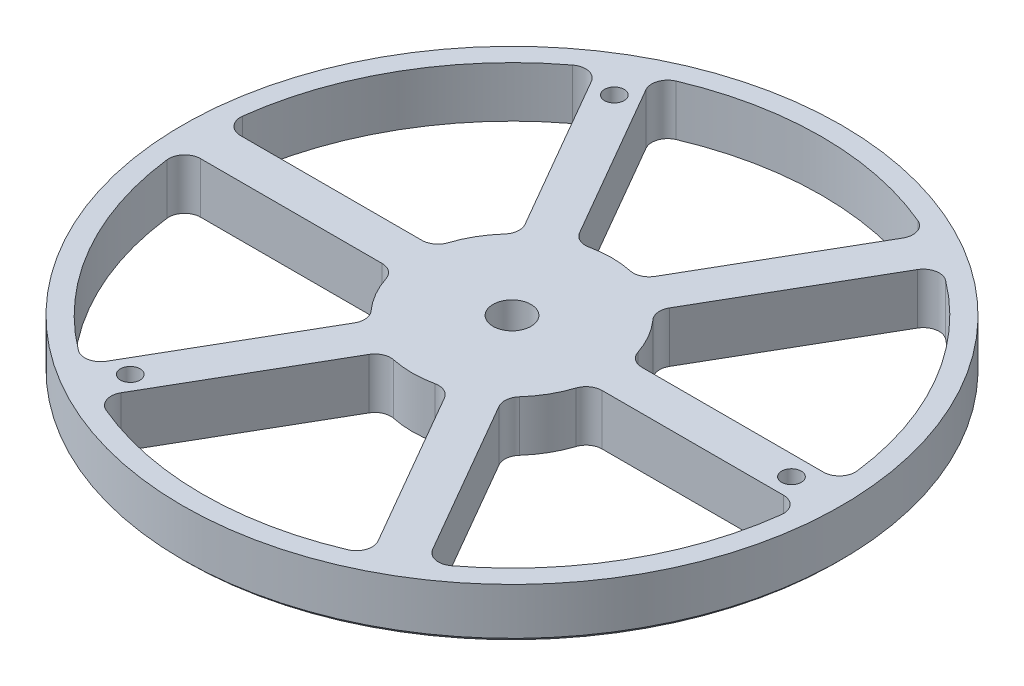
SolidWorks part; units mm, degrees
material "6061-T6 (SS)"
ref_plane "Front Plane" through (0, 0, 0) normal (0, 0, 1) x (1, 0, 0)
ref_plane "Top Plane" through (0, 0, 0) normal (0, 1, 0) x (1, 0, 0)
ref_plane "Right Plane" through (0, 0, 0) normal (1, 0, 0) x (0, 0, -1)
sketch "Sketch2" plane through (0, 0, 0) normal (1, 0, 0) x (0, 0, -1)
  line L0 (0, 0) -> (-82.55, 0)
  line L1 (-82.55, 0) -> (-82.55, 12.7)
  line L2 (-82.55, 12.7) -> (0, 12.7)
  line L5 (0, 12.7) -> (0, 0)
  dimension "D1" = 82.55
  dimension "D2" = 12.7
ref_axis "Axis1" through (0, -0.635, 0) along (0, 1, 0)
revolve "Revolve1" add sketch "Sketch2" angle 360 about axis through (0, -0.635, 0) along (0, 1, 0)
hole_wizard "#10 (0.1935) Diameter Hole1" positions "Sketch6" profile "Sketch7" hole size "#10" standard "ANSI Inch" end condition through all
sketch "Sketch6" plane through (0, 12.7, 0) normal (0, 1, 0) x (1, 0, 0)
  line L0 (0, 0) -> (-69.8201, 120.932) construction
  line L2 (0, 0) -> (0, 109.0908) construction
  point P0 (-35, 60.6218)
  dimension "D1" = 30
  dimension "D2" = 70
sketch "Sketch7" plane through (-35, 12.7, -60.6218) normal (1, 0, 0) x (0, 0, 1)
  line L0 (0, 0) -> (0, 12.7)
  line L1 (0, 12.7) -> (2.4574, 12.7)
  line L2 (2.4574, 12.7) -> (2.4574, 0)
  line L5 (2.4574, 0) -> (0, 0)
  line L11 (0, -6.35) -> (0, 107.95) construction
  dimension "Thru Hole Dia." = 4.9149
  dimension "Thru Hole Depth" = 12.7
pattern_circular "CirPattern3" count 3 over 360 about axis through (0, 0, 0) along (0, 1, 0) of "#10 (0.1935) Diameter Hole1"
sketch "Sketch8" plane through (0, 12.7, 0) normal (0, 1, 0) x (1, 0, 0)
  line L4 (0, 0) -> (0, 93.9995) construction
  line L5 (0, 0) -> (113.8372, 0) construction
  line L6 (-7.9173, 23.7132) -> (-34.3642, 69.5205)
  line L7 (7.9173, 23.7132) -> (34.3642, 69.5205)
  line L8 (0, 0) -> (-35, 60.6218) construction
  arc A0 (-7.9173, 23.7132) -> (7.9173, 23.7132) centre (0, 0) cw
  arc A1 (-34.3642, 69.5205) -> (34.3642, 69.5205) centre (0, 0) cw
  circle A2 centre (0, 0) radius 82.55 construction
  dimension "D1" = 25
  dimension "D2" = 5
  dimension "D3" = 5
extrude "Cut-Extrude1" cut sketch "Sketch8" against normal through all
fillet "Fillet1" radius 4 4 edges at (7.9173, 6.35, -23.7132) (34.3642, 6.35, -69.5205) (-7.9173, 6.35, -23.7132) (-34.3642, 6.35, -69.5205)
pattern_circular "CirPattern4" count 6 over 360 about axis through (0, 0, 0) along (0, 1, 0) of "Cut-Extrude1", "Fillet1"
chamfer "Chamfer2" distance 1 angle 45 1 edges at (0, 0, -82.55)
hole_wizard "3/8 (0.375) Diameter Hole1" positions "Sketch9" profile "Sketch11" hole size "3/8" standard "ANSI Inch" end condition through all
sketch "Sketch9" plane through (0, 0, 0) normal (0, -1, 0) x (-1, 0, 0)
  point P0 (0, 0)
sketch "Sketch11" plane through (0, 0, 0) normal (1, 0, 0) x (0, 0, -1)
  line L0 (0, 0) -> (0, 12.7)
  line L1 (0, 12.7) -> (4.7625, 12.7)
  line L2 (4.7625, 12.7) -> (4.7625, 0)
  line L5 (4.7625, 0) -> (0, 0)
  line L11 (0, -6.35) -> (0, 107.95) construction
  dimension "Thru Hole Dia." = 9.525
  dimension "Thru Hole Depth" = 12.7
equation "\"TubeDiameter\"= 6.500in"
equation "\"D1@Sketch2\"=\"TubeDiameter\"/2"
